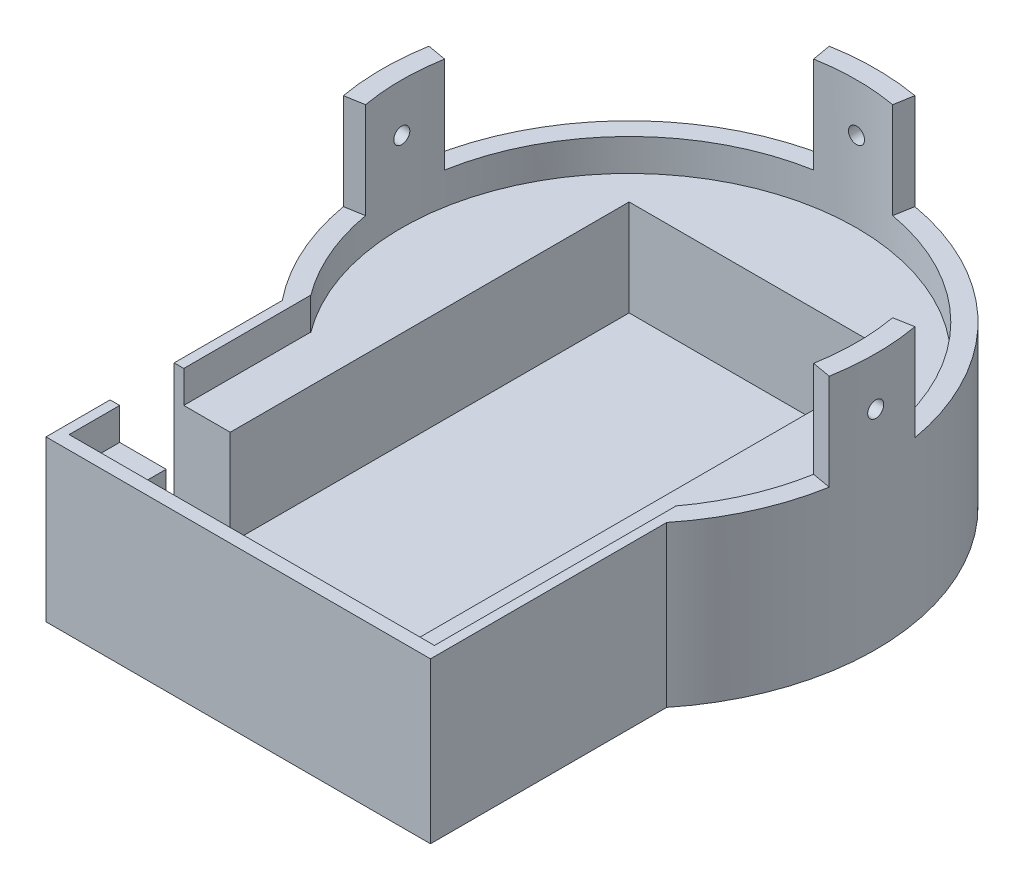
SolidWorks part; units mm, degrees
ref_plane "Спереди" through (0, 0, 0) normal (0, 0, 1) x (1, 0, 0)
ref_plane "Сверху" through (0, 0, 0) normal (0, 1, 0) x (1, 0, 0)
ref_plane "Справа" through (0, 0, 0) normal (1, 0, 0) x (0, 0, -1)
sketch "Эскиз1" plane through (0, 0, 0) normal (0, 1, 0) x (1, 0, 0)
  line L0 (-60, -74.6139) -> (-60, -48.2597)
  line L2 (60, -74.6139) -> (60, -48.2597)
  line L3 (-60, -74.6139) -> (-60, -122)
  line L4 (-60, -122) -> (60, -122)
  line L5 (60, -122) -> (60, -74.6139)
  arc A0 (60, -48.2597) -> (-60, -48.2597) centre (0, 0) ccw
  point P7 (0, -77)
  dimension "D1" = 154
  dimension "D2" = 120
  dimension "D3" = 26.3542
  dimension "D4" = 45
  dimension "D5" = 60
extrude "Бобышка-Вытянуть1" add sketch "Эскиз1" along normal blind 50
sketch "Эскиз2" plane through (0, 50, 0) normal (0, 1, 0) x (1, 0, 0)
  line L1 (-42.5, 42.5) -> (42.5, 42.5)
  line L2 (-42.5, 42.5) -> (-42.5, -42.5)
  line L3 (-42.5, -42.5) -> (42.5, -42.5)
  line L4 (42.5, 42.5) -> (42.5, -42.5)
  line L5 (-42.5, 42.5) -> (42.5, -42.5) construction
  line L6 (-42.5, -42.5) -> (42.5, 42.5) construction
  point P0 (0, 0)
  dimension "D1" = 85
  dimension "D2" = 85
extrude "Вырез-Вытянуть1" cut sketch "Эскиз2" against normal blind 40
sketch "Эскиз3" plane through (0, 50, 0) normal (0, 1, 0) x (1, 0, 0)
  circle A0 centre (0, 0) radius 71
  dimension "140" = 142
extrude "Вырез-Вытянуть2" cut sketch "Эскиз3" against normal blind 10
sketch "Эскиз4" plane through (0, 50, 0) normal (0, 1, 0) x (1, 0, 0)
  line L0 (0, 77) -> (0, 71)
  line L1 (-12.329, 69.9214) -> (-13.3709, 75.8302)
  line L2 (0, -71) -> (0, -77)
  circle A0 centre (0, 0) radius 77
  circle A1 centre (0, 0) radius 71
  circle M4 centre (0, 0) radius 71
  arc M5 (60, -48.2597) -> (-60, -48.2597) centre (0, 0) ccw
  dimension "D1" = 154
  dimension "D2" = 142
  dimension "D4" = 5.9088
  dimension "D3" = 10
extrude "Бобышка-Вытянуть2" add sketch "Эскиз4" along normal blind 30 contours L1 L0 M4 M5
mirror "Зеркальное отражение1" about plane through (0, 0, 0) normal (1, 0, 0) of "Бобышка-Вытянуть2"
sketch "Эскиз5" plane through (0, 0, 0) normal (1, 0, 0) x (0, 0, -1)
  line L0 (0, 0) -> (0, 100) construction
  dimension "D1" = 100
pattern_circular "Круговой массив1" count 4 over 360 about axis through (0, 0, 0) along (0, 1, 0) skipping 2 of "Бобышка-Вытянуть2", "Зеркальное отражение1"
ref_plane "Плоскость1" through (0, 0, -70) normal (0, 0, 1) x (1, 0, 0)
sketch "Эскиз8" plane through (0, 0, -70) normal (0, 0, 1) x (1, 0, 0)
  line L0 (0, 0) -> (0, 65) construction
  circle A0 centre (0, 65) radius 2.5
  dimension "D2" = 5
  dimension "D1" = 65
extrude "Вырез-Вытянуть3" cut sketch "Эскиз8" against normal blind 30
pattern_circular "Круговой массив2" count 4 over 360 about axis through (0, 0, 0) along (0, 1, 0) of "Вырез-Вытянуть3"
sketch "Эскиз9" plane through (0, 50, 0) normal (0, 1, 0) x (1, 0, 0)
  line L0 (0, 0) -> (0, -121.8823) construction
  line L1 (0, -71) -> (-60.1996, -71) construction
  line L2 (-57, -68) -> (-57, -42.5)
  line L3 (-42.5, -42.5) -> (42.5, -42.5) construction
  line L4 (-57, -42.5) -> (57, -42.5)
  line L5 (57, -42.5) -> (57, -124)
  line L6 (57, -124) -> (-57, -124)
  line L7 (-57, -124) -> (-57, -68)
  arc A2 (-69.9214, -12.329) -> (69.9214, -12.329) centre (0, 0) ccw construction
  dimension "D4" = 53
  dimension "D1" = 114
  dimension "D2" = 57
extrude "Вырез-Вытянуть4" cut sketch "Эскиз9" against normal blind 10
sketch "Эскиз10" plane through (0, 40, 0) normal (0, 1, 0) x (1, 0, 0)
  line L0 (0, 0) -> (0, -121.3479) construction
  line L1 (-42.5, -42.5) -> (-42.5, -117.7589)
  line L2 (-42.5, -117.7589) -> (42.5, -117.7589)
  line L3 (42.5, -117.7589) -> (42.5, -42.5)
  line L4 (42.5, -42.5) -> (-42.5, -42.5) construction
  line L5 (-42.5, -42.5) -> (42.5, -42.5)
  dimension "D1" = 85
  dimension "D2" = 75.2589
extrude "Вырез-Вытянуть6" cut sketch "Эскиз10" against normal blind 30
sketch "Эскиз11" plane through (0, 40, 0) normal (0, 1, 0) x (1, 0, 0)
  line L0 (57, -122) -> (-57, -122) construction
  line L3 (-57, -117.76) -> (-57, -122)
  line L4 (57, -122) -> (57, -42.5) construction
  line L5 (57, -117.76) -> (-57, -117.76)
  line L6 (-57, -42.5) -> (-57, -122) construction
  line L7 (-57, -122) -> (57, -122)
  line L8 (57, -122) -> (57, -117.76)
  dimension "D1" = 4.24
extrude "Бобышка-Вытянуть3" add sketch "Эскиз11" along normal blind 10
sketch "Эскиз12" plane through (0, 50, 0) normal (0, 1, 0) x (1, 0, 0)
  line L0 (-76.628, -82) -> (-36.628, -82)
  line L2 (-36.628, -82) -> (-36.628, -102)
  line L3 (-36.628, -102) -> (-76.628, -102)
  line L4 (-76.628, -102) -> (-76.628, -82)
  line L5 (-60, -122) -> (60, -122) construction
  dimension "D1" = 20
  dimension "20" = 20
  dimension "D2" = 40
extrude "Вырез-Вытянуть7" cut sketch "Эскиз12" against normal blind 40
